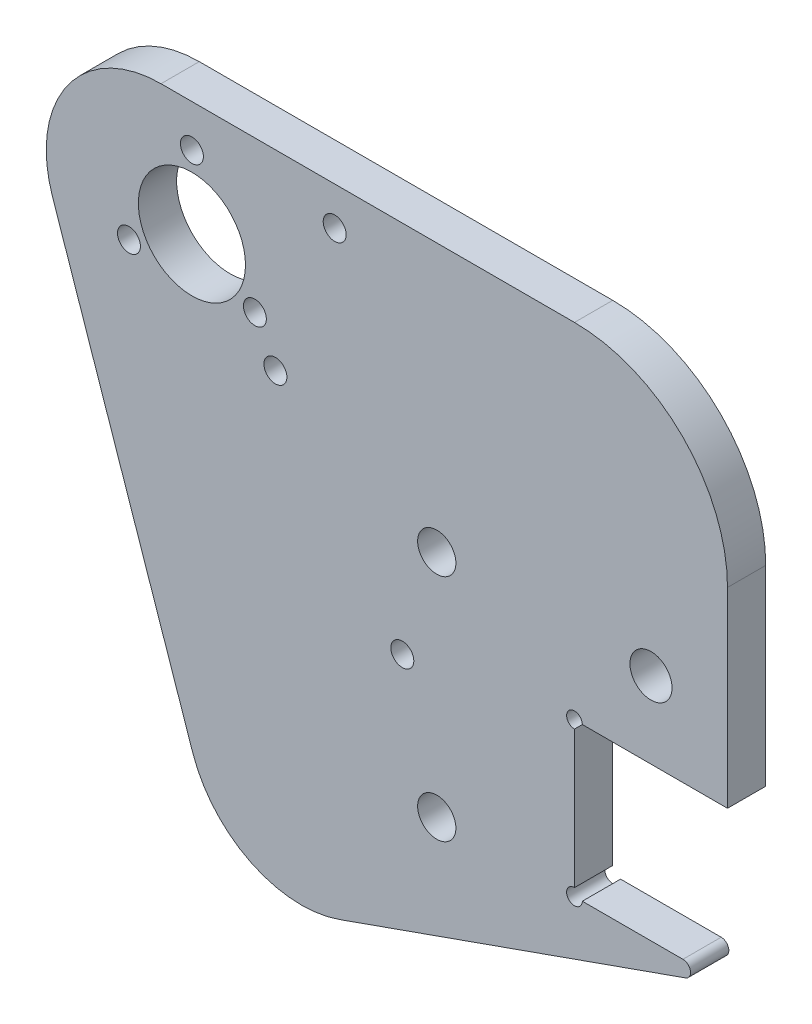
SolidWorks part; units mm, degrees
material "Thornel Mat VMA"
ref_plane "前视基准面" through (0, 0, 0) normal (0, 0, 1) x (1, 0, 0)
ref_plane "上视基准面" through (0, 0, 0) normal (0, 1, 0) x (1, 0, 0)
ref_plane "右视基准面" through (0, 0, 0) normal (1, 0, 0) x (0, 0, -1)
sketch "草图1" plane through (0, 0, 0) normal (0, 0, 1) x (1, 0, 0)
  line L0 (70, -30) -> (70, -5)
  line L1 (50, -50) -> (70, -50)
  line L2 (50, -50) -> (50, -30)
  line L3 (50, -30) -> (70, -30)
  line L4 (70, -50) -> (70, -30) construction
  line L5 (60, -30) -> (60, -50) construction
  line L6 (50, -40) -> (70, -40) construction
  line L7 (50, 15) -> (-4.0387, 15)
  line L8 (-18.2363, -4.8401) -> (0.1037, -58.6375)
  line L9 (19.305, -67.9382) -> (70, -50)
  circle A0 centre (0, 0) radius 7
  circle A1 centre (0, 0) radius 9.5 construction
  circle A2 centre (0, 9.5) radius 1.5
  circle A3 centre (8.2272, -4.75) radius 1.5
  circle A4 centre (-8.2272, -4.75) radius 1.5
  circle A5 centre (32, -50) radius 2.5
  arc A8 (70, -5) -> (50, 15) centre (50, -5) ccw
  arc A9 (-4.0387, 15) -> (-18.2363, -4.8401) centre (-4.0387, 0) ccw
  arc A10 (0.1037, -58.6375) -> (19.305, -67.9382) centre (14.3013, -53.7974) ccw
  circle A11 centre (32, -20) radius 2.5
  point P13 (0, 0)
  point P29 (70, 15)
  point P32 (-25, 15)
  point P35 (5, -73)
  point P39 (60, -40)
  dimension "D1" = 14
  dimension "D2" = 19
  dimension "D3" = 3
  dimension "D9" = 5
  dimension "D12" = 10
  dimension "D18" = 20
  dimension "D19" = 15
  dimension "D20" = 15
  dimension "D5" = 20
  dimension "D6" = 20
  dimension "D7" = 50
  dimension "D8" = 30
  dimension "D10" = 18
  dimension "D14" = 45
  dimension "D15" = 95
  dimension "D16" = 23
  dimension "D17" = 65
  dimension "D4" = 3
extrude "凸台-拉伸1" add sketch "草图1" along normal blind 5
fillet "圆角1" radius 1 1 edges at (70, -50, 2.5)
sketch "草图2" plane through (0, 0, 5) normal (0, 0, 1) x (1, 0, 0)
  line L0 (50, -30) -> (70, -30) construction
  line L1 (50, -50) -> (50, -30) construction
  circle A0 centre (27.5, -33.82) radius 1.5
  circle A1 centre (18.66, 10) radius 1.5
  circle A2 centre (60, -20) radius 2.75 construction
  circle A3 centre (60, -20) radius 2.75
  dimension "D1" = 3
  dimension "D2" = 3
  dimension "D3" = 40
  dimension "D4" = 31.34
  dimension "D5" = 22.5
  dimension "D6" = 3.82
extrude "切除-拉伸1" cut sketch "草图2" against normal blind 10
sketch "草图3" plane through (0, 0, 5) normal (0, 0, 1) x (1, 0, 0)
  line L0 (70, -30) -> (70, -5) construction
  line L3 (50, 15) -> (-4.0387, 15) construction
  circle A0 centre (10.9144, -10) radius 2.5
  circle A1 centre (10.9144, -10) radius 1.5
  dimension "D1" = 5
  dimension "D4" = 3
  dimension "D3" = 59.0856
  dimension "D2" = 25
extrude "切除-拉伸2" cut sketch "草图3" against normal blind 10 contours A1
sketch "草图4" plane through (0, 0, 0) normal (0, 0, -1) x (-1, 0, 0)
  circle A0 centre (-50, -50) radius 1.025
  circle A1 centre (-50, -30) radius 1.025
  dimension "D1" = 2.05
extrude "切除-拉伸3" cut sketch "草图4" against normal mid plane 60
